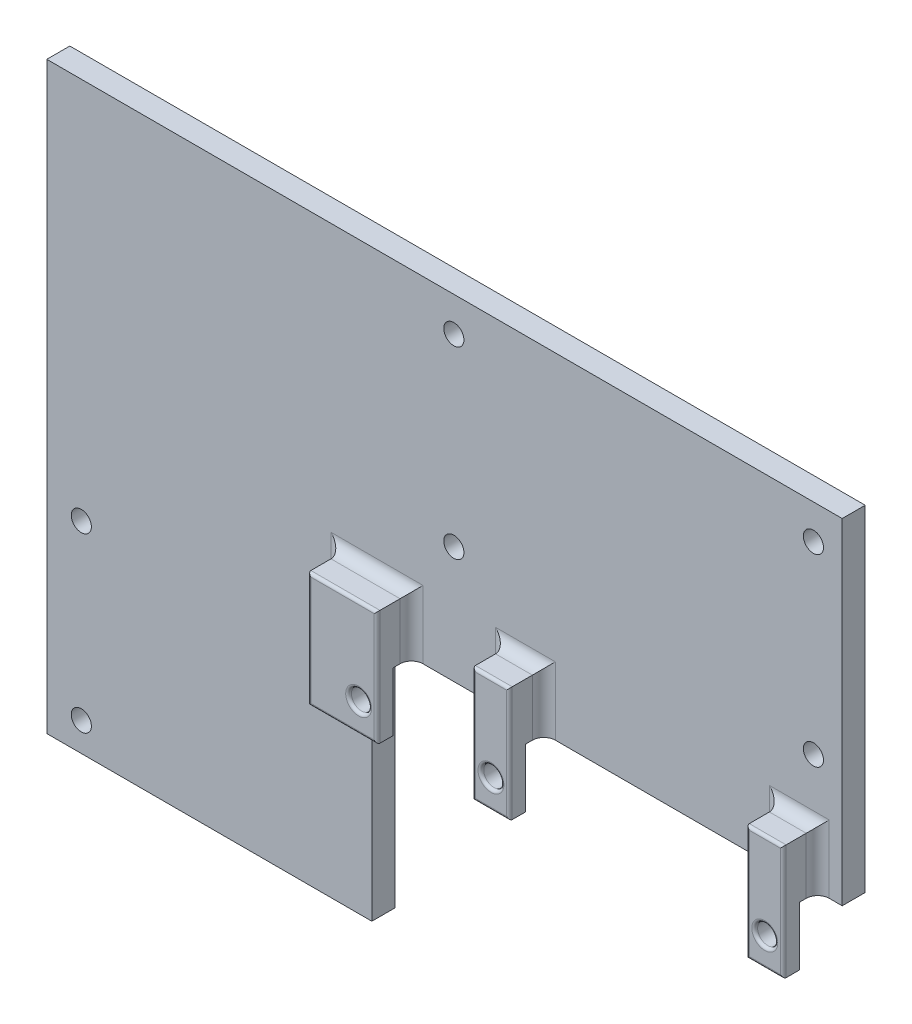
SolidWorks part; units mm, degrees
ref_plane "正面" through (0, 0, 0) normal (0, 0, 1) x (1, 0, 0)
ref_plane "平面" through (0, 0, 0) normal (0, 1, 0) x (1, 0, 0)
ref_plane "右側面" through (0, 0, 0) normal (1, 0, 0) x (0, 0, -1)
sketch "ｽｹｯﾁ1" plane through (0, 0, 0) normal (0, 0, 1) x (1, 0, 0)
  line L1 (-69.125, -50.75) -> (69.125, -50.75)
  line L2 (-69.125, -50.75) -> (-69.125, 50.75)
  line L3 (-69.125, 50.75) -> (69.125, 50.75)
  line L4 (69.125, -50.75) -> (69.125, 50.75)
  line L5 (-69.125, -50.75) -> (69.125, 50.75) construction
  line L6 (-69.125, 50.75) -> (69.125, -50.75) construction
  point P0 (0, 0)
  dimension "D1" = 138.25
  dimension "D2" = 101.5
extrude "ﾎﾞｽ - 押し出し1" add sketch "ｽｹｯﾁ1" along normal blind 4
sketch "ｽｹｯﾁ2" plane through (0, 0, 4) normal (0, 0, 1) x (1, 0, 0)
  line L1 (69.125, -50.75) -> (-12.625, -50.75)
  line L2 (69.125, -50.75) -> (69.125, -7.55)
  line L3 (69.125, -7.55) -> (-12.625, -7.55)
  line L4 (-12.625, -50.75) -> (-12.625, -7.55)
  dimension "D1" = 81.75
  dimension "D2" = 43.2
extrude "ｶｯﾄ - 押し出し1" cut sketch "ｽｹｯﾁ2" against normal through all
sketch "ｽｹｯﾁ3" plane through (0, 0, 4) normal (0, 0, 1) x (1, 0, 0)
  line L0 (-69.125, -50.75) -> (-12.625, -50.75) construction
  line L1 (-69.125, 50.75) -> (-69.125, -50.75) construction
  line L2 (69.125, 50.75) -> (-69.125, 50.75) construction
  line L3 (69.125, -7.55) -> (69.125, 50.75) construction
  circle A0 centre (-63.125, -45.75) radius 1.75
  circle A1 centre (-63.125, -15.75) radius 1.75
  circle A2 centre (64.125, 44.75) radius 1.75
  circle A3 centre (64.125, 12.75) radius 1.75
  circle A4 centre (1.625, 44.75) radius 1.75
  circle A5 centre (1.625, 12.75) radius 1.75
  dimension "D3" = 3.5
  dimension "D4" = 3.5
  dimension "D6" = 3.5
  dimension "D9" = 3.5
  dimension "D12" = 3.5
  dimension "D13" = 3.5
  dimension "D1" = 5
  dimension "D2" = 6
  dimension "D5" = 30
  dimension "D7" = 6
  dimension "D8" = 5
  dimension "D10" = 32
  dimension "D11" = 62.5
extrude "ｶｯﾄ - 押し出し2" cut sketch "ｽｹｯﾁ3" against normal through all
sketch "ｽｹｯﾁ4" plane through (0, 0, 4) normal (0, 0, 1) x (1, 0, 0)
  line L0 (69.125, 50.75) -> (-69.125, 50.75) construction
  line L1 (69.125, -7.55) -> (69.125, 50.75) construction
  line L3 (64.875, 2.25) -> (58.475, 2.25)
  line L4 (64.875, 2.25) -> (64.875, -17.75)
  line L5 (64.875, -17.75) -> (58.475, -17.75)
  line L6 (58.475, 2.25) -> (58.475, -17.75)
  line L7 (17.275, 2.25) -> (10.875, 2.25)
  line L8 (17.275, 2.25) -> (17.275, -17.75)
  line L9 (17.275, -17.75) -> (10.875, -17.75)
  line L10 (10.875, 2.25) -> (10.875, -17.75)
  line L12 (-5.725, 2.25) -> (-17.725, 2.25)
  line L13 (-5.725, 2.25) -> (-5.725, -17.75)
  line L14 (-5.725, -17.75) -> (-17.725, -17.75)
  line L15 (-17.725, 2.25) -> (-17.725, -17.75)
  circle A0 centre (-8.925, -12.75) radius 1.75
  circle A1 centre (14.075, -12.75) radius 1.75
  circle A2 centre (61.675, -12.75) radius 1.75
  dimension "D1" = 3.5
  dimension "D4" = 3.5
  dimension "D7" = 3.5
  dimension "D2" = 63.5
  dimension "D3" = 78.05
  dimension "D5" = 23
  dimension "D6" = 47.6
  dimension "D8" = 3.2
  dimension "D9" = 6.4
  dimension "D10" = 20
  dimension "D11" = 5
  dimension "D12" = 20
  dimension "D13" = 0
  dimension "D14" = 3.2
  dimension "D15" = 6.4
  dimension "D16" = 3.2
  dimension "D17" = 12
extrude "ﾎﾞｽ - 押し出し6" add sketch "ｽｹｯﾁ4" along normal blind 6
fillet "ﾌｨﾚｯﾄ3" radius 2 9 edges at (61.675, 2.25, 4) (64.875, -2.65, 4) (58.475, -2.65, 4) (-5.725, -2.65, 4) (-17.725, -7.75, 4) (-11.725, 2.25, 4) (10.875, -2.65, 4) (17.275, -2.65, 4) (14.075, 2.25, 4)
sketch "ｽｹｯﾁ5" plane through (69.125, 0, 0) normal (1, 0, 0) x (0, 0, -1)
  line L0 (-10, -17.75) -> (-4, -17.75) construction
  line L1 (-4, -7.55) -> (-7.2, -7.55)
  line L2 (-4, -7.55) -> (-4, -17.75)
  line L3 (-4, -17.75) -> (-7.2, -17.75)
  line L4 (-7.2, -7.55) -> (-7.2, -17.75)
  dimension "D1" = 3.2
extrude "ｶｯﾄ - 押し出し3" cut sketch "ｽｹｯﾁ5" against normal blind 81.75
fillet "ﾌｨﾚｯﾄ4" radius 0.5 15 edges at (63.425, -12.75, 10) (61.675, -17.75, 10) (58.475, -7.75, 10) (61.675, 2.25, 10) (64.875, -7.75, 10) (15.825, -12.75, 10) (14.075, -17.75, 10) (10.875, -7.75, 10) (14.075, 2.25, 10) (17.275, -7.75, 10) (-7.175, -12.75, 10) (-11.725, -17.75, 10) (-17.725, -7.75, 10) (-11.725, 2.25, 10) (-5.725, -7.75, 10)
